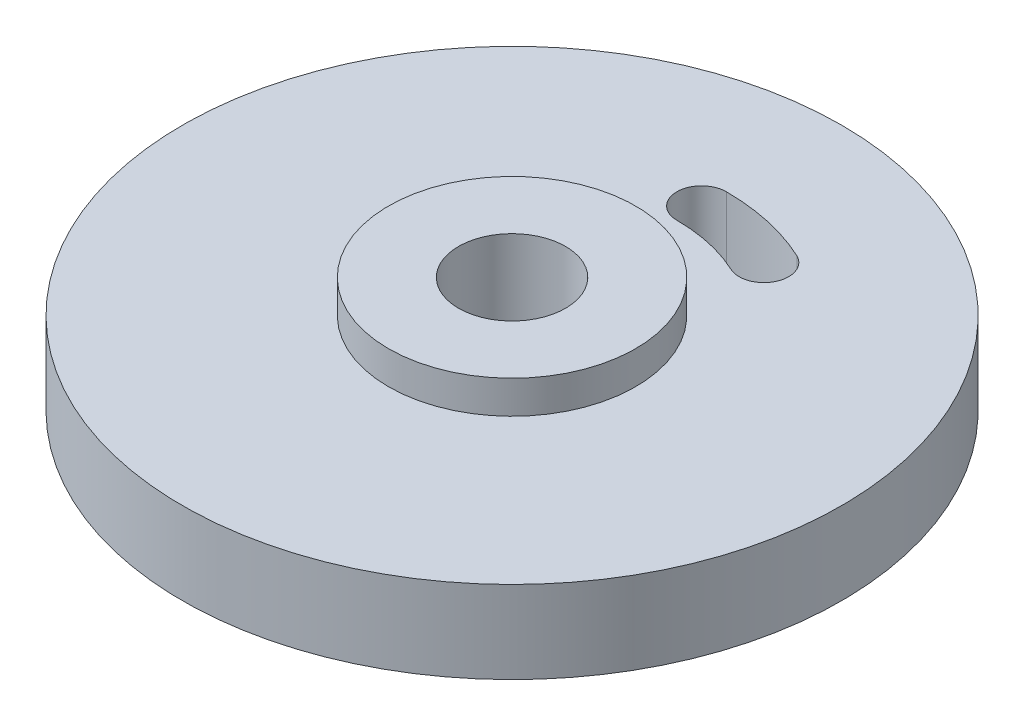
SolidWorks part; units mm, degrees
ref_plane "Plano frontal" through (0, 0, 0) normal (0, 0, 1) x (1, 0, 0)
ref_plane "Plano superior" through (0, 0, 0) normal (0, 1, 0) x (1, 0, 0)
ref_plane "Plano direito" through (0, 0, 0) normal (1, 0, 0) x (0, 0, -1)
sketch "Esboço1" plane through (0, 0, 0) normal (0, 0, 1) x (1, 0, 0)
  line L0 (0, 0) -> (0, 22.7862) construction
  line L1 (0, 0) -> (19.7974, 0) construction
  line L2 (3.25, 14) -> (3.25, 11.5)
  line L3 (3.25, 11.5) -> (5, 11.5)
  line L4 (5, 11.5) -> (5, 9)
  line L5 (5, 9) -> (20, 9)
  line L6 (20, 14) -> (20, 9)
  line L9 (20, 14) -> (3.25, 14)
  dimension "D2" = 16.75
  dimension "D3" = 5
  dimension "D5" = 10
  dimension "D6" = 6.5
  dimension "D8" = 9
  dimension "D10" = 2.5
revolve "Revolução1" add sketch "Esboço1" angle 360 about L0
sketch "Esboço2" plane through (0, 0, 0) normal (0, 1, 0) x (1, 0, 0)
  line L0 (0, 13) -> (0, 10) construction
  line L1 (4.2262, 9.0631) -> (5.494, 11.782) construction
  arc A0 (4.2262, 9.0631) -> (0, 10) centre (0, 0) ccw
  arc A1 (5.494, 11.782) -> (0, 13) centre (0, 0) ccw
  arc A2 (0, 13) -> (0, 10) centre (0, 11.5) ccw
  arc A3 (5.494, 11.782) -> (4.2262, 9.0631) centre (4.8601, 10.4225) cw
  dimension "D1" = 20
  dimension "D2" = 26
  dimension "D3" = 25
ref_plane "Plano1" through (0, 9, 0) normal (0, -1, 0) x (-1, 0, 0)
extrude "Corte-extrusão3" cut sketch "Esboço2" along normal up to next
ref_plane "Plano2" through (0, 14, 0) normal (0, 1, 0) x (1, 0, 0)
sketch "Esboço4" plane through (0, 14, 0) normal (0, 1, 0) x (1, 0, 0)
  circle A0 centre (0, 0) radius 3.25
  circle A1 centre (0, 0) radius 7.5
  dimension "D1" = 6.5
  dimension "D2" = 15
extrude "Ressalto-extrusão1" add sketch "Esboço4" along normal blind 2 and the other way blind 7
